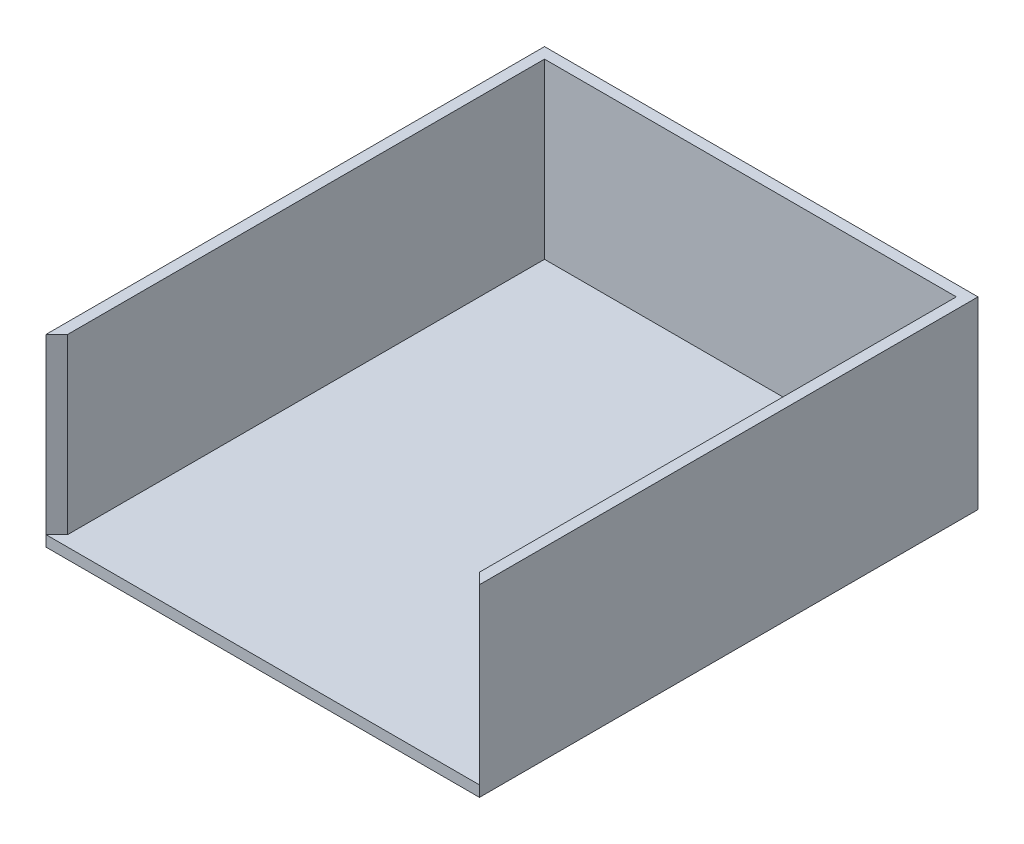
SolidWorks part; units mm, degrees
ref_plane "Front Plane" through (0, 0, 0) normal (0, 0, 1) x (1, 0, 0)
ref_plane "Top Plane" through (0, 0, 0) normal (0, 1, 0) x (1, 0, 0)
ref_plane "Right Plane" through (0, 0, 0) normal (1, 0, 0) x (0, 0, -1)
sketch "Sketch1" plane through (0, 0, 0) normal (0, 1, 0) x (1, 0, 0)
  line L1 (-100, -115) -> (100, -115)
  line L2 (-100, -115) -> (-100, 115)
  line L3 (-100, 115) -> (100, 115)
  line L4 (100, -115) -> (100, 115)
  line L5 (-100, -115) -> (100, 115) construction
  line L6 (-100, 115) -> (100, -115) construction
  point P0 (0, 0)
  dimension "D1" = 200
  dimension "D2" = 230
extrude "Boss-Extrude1" add sketch "Sketch1" along normal blind 5
sketch "Sketch2" plane through (0, 5, 0) normal (0, 1, 0) x (1, 0, 0)
  line L4 (100, -115) -> (100, 115)
  line L5 (100, 115) -> (-100, 115)
  line L6 (-100, 115) -> (-100, -115)
  line L7 (-100, -115) -> (100, -115)
  line L8 (100, -115) -> (100, 115)
  line L9 (100, 115) -> (-100, 115)
  line L10 (-100, 115) -> (-100, -115)
  line L11 (-100, -115) -> (-95, -110)
  line L12 (100, -115) -> (95, -110)
  line L16 (95, -110) -> (95, 110)
  line L17 (95, 110) -> (-95, 110)
  line L18 (-95, 110) -> (-95, -110)
  line L19 (-95, -110) -> (95, -110)
  line L20 (95, -110) -> (95, 110)
  line L21 (95, 110) -> (-95, 110)
  line L22 (-95, 110) -> (-95, -110)
  dimension "D1" = 0
  dimension "D2" = 5
extrude "Boss-Extrude2" add sketch "Sketch2" along normal blind 80
